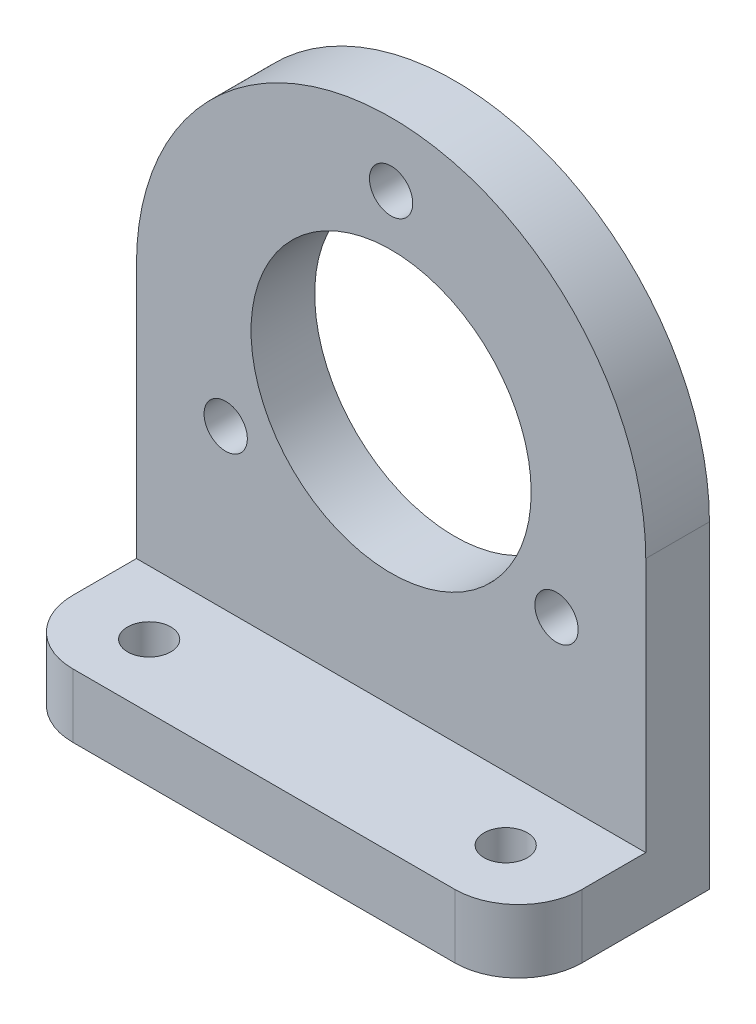
SolidWorks part; units mm, degrees
ref_plane "Front Plane" through (0, 0, 0) normal (0, 0, 1) x (1, 0, 0)
ref_plane "Top Plane" through (0, 0, 0) normal (0, 1, 0) x (1, 0, 0)
ref_plane "Right Plane" through (0, 0, 0) normal (1, 0, 0) x (0, 0, -1)
sketch "Sketch1" plane through (0, 0, 0) normal (0, 0, 1) x (1, 0, 0)
  line L1 (-20, 20) -> (20, 20)
  line L2 (-20, 20) -> (-20, -20)
  line L3 (-20, -20) -> (20, -20)
  line L4 (20, 20) -> (20, -20)
  line L5 (-20, 20) -> (20, -20) construction
  line L6 (-20, -20) -> (20, 20) construction
  circle A0 centre (0, 0) radius 20
  circle A1 centre (0, 0) radius 11
  point P0 (0, 0)
  dimension "D3" = 22
  dimension "D1" = 40
  dimension "D2" = 40
extrude "Boss-Extrude1" add sketch "Sketch1" along normal blind 5 contours A0 | A0 L3 L4 | A0 L2 L3
sketch "Sketch2" plane through (0, 0, 5) normal (0, 0, 1) x (1, 0, 0)
  point P0 (0, 15)
  dimension "D1" = 15
hole_wizard "M3 Clearance Hole1" positions "3DSketch1" profile "Sketch4" hole size "M3" standard "ISO"
sketch3d "3DSketch1"
  point P0 (0, 15, 5)
sketch "Sketch4" plane through (0, 15, 5) normal (1, 0, 0) x (0, -1, 0)
  line L0 (0, 0) -> (0, 6.0205)
  line L1 (0, 6.0205) -> (1.7, 4.999)
  line L2 (1.7, 4.999) -> (1.7, 0)
  line L5 (1.7, 0) -> (0, 0)
  line L10 (0, 6.0205) -> (-1.7, 4.999) construction
  line L11 (0, -6.35) -> (0, 107.95) construction
  dimension "Hole Dia." = 3.4
  dimension "Hole Depth" = 4.999
  dimension "Drill Angle" = 118
pattern_circular "CirPattern1" count 3 over 360 about axis through (0, 0, 0) along (0, 0, 1) of "M3 Clearance Hole1"
sketch "Sketch5" plane through (0, 0, 0) normal (0, 0, 1) x (1, 0, 0)
  line L0 (20, 0) -> (20, -20) construction
  line L1 (-20, -20) -> (20, -20)
  line L2 (-20, -20) -> (-20, -25)
  line L3 (-20, -25) -> (20, -25)
  line L4 (20, -20) -> (20, -25)
  dimension "D1" = 5
extrude "Boss-Extrude2" add sketch "Sketch5" along normal blind 15
sketch "Sketch8" plane through (0, -20, 0) normal (0, 1, 0) x (1, 0, 0)
  line L0 (-20, -15) -> (-20, -5) construction
  line L1 (20, -15) -> (20, -5) construction
  point P0 (-14, -10)
  point P1 (14, -10)
  point P6 (-20, -10)
  dimension "D1" = 6
  dimension "D2" = 6
hole_wizard "M3 Clearance Hole3" positions "3DSketch3" profile "Sketch9" hole size "M3" standard "ISO"
sketch3d "3DSketch3"
  point P0 (-14, -20, 10)
  point P3 (14, -20, 10)
sketch "Sketch9" plane through (-14, -20, 10) normal (1, 0, 0) x (0, 0, 1)
  line L0 (0, 0) -> (0, 6.0205)
  line L1 (0, 6.0205) -> (1.7, 4.999)
  line L2 (1.7, 4.999) -> (1.7, 0)
  line L5 (1.7, 0) -> (0, 0)
  line L10 (0, 6.0205) -> (-1.7, 4.999) construction
  line L11 (0, -6.35) -> (0, 107.95) construction
  dimension "Hole Dia." = 3.4
  dimension "Hole Depth" = 4.999
  dimension "Drill Angle" = 118
fillet "Fillet1" radius 5 2 edges at (20, -22.5, 15) (-20, -22.5, 15)
equation "\"H\"= 40mm'height"
equation "\"T\"= 5mm'thickness"
equation "\"D1@Boss-Extrude1\"=\"T\""
equation "\"D1@Sketch5\"=\"T\""
